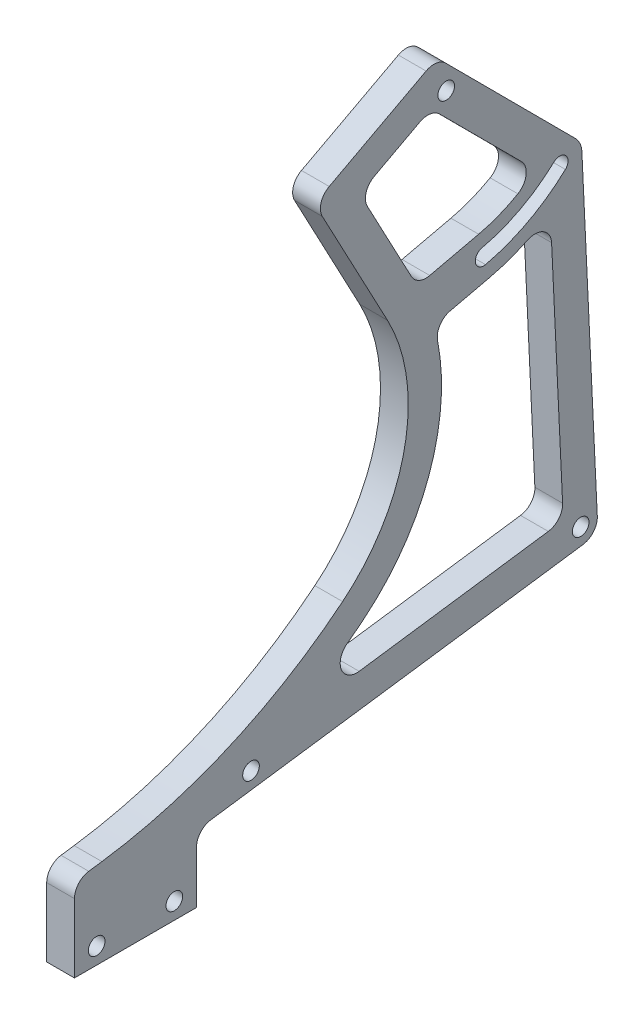
SolidWorks part; units mm, degrees
ref_plane "Front Plane" through (0, 0, 0) normal (0, 0, 1) x (1, 0, 0)
ref_plane "Top Plane" through (0, 0, 0) normal (0, 1, 0) x (1, 0, 0)
ref_plane "Right Plane" through (0, 0, 0) normal (1, 0, 0) x (0, 0, -1)
sketch "Sketch1" plane through (0, 0, 0) normal (1, 0, 0) x (0, 0, -1)
  line L0 (0, 0) -> (0, 15)
  line L1 (0, 15) -> (94.0755, 28.2214) construction
  line L2 (94.0755, 28.2214) -> (94.362, 22.2028)
  line L3 (94.362, 22.2028) -> (22, 12.0329)
  line L5 (22, 12.0329) -> (22, 0)
  line L6 (22, 0) -> (0, 0)
  line L11 (73.7485, 75.7689) -> (67, 105) construction
  line L12 (67, 105) -> (87.46, 83.0594) construction
  line L13 (0, 15) -> (4.9513, 15.6959)
  line L14 (65.3411, 110.9134) -> (43.2674, 99.1766)
  line L15 (43.2674, 99.1766) -> (56.4126, 74.4541)
  line L17 (65.3411, 110.9134) -> (90.2928, 85.8834)
  line L18 (67, 105) -> (81.0841, 78.5116) construction
  line L19 (49.84, 86.8153) -> (81.3511, 103.5701) construction
  line L20 (91.4554, 83.2496) -> (94.0755, 28.2214)
  line L21 (37.7341, 20.3032) -> (88.1086, 27.3829)
  line L22 (88.1086, 27.3829) -> (85.763, 76.646)
  line L23 (83.1087, 84.5914) -> (64.2314, 103.5279)
  line L24 (64.2314, 103.5279) -> (51.382, 96.6957)
  line L25 (51.382, 96.6957) -> (61.7937, 77.1141)
  line L26 (61.7937, 77.1141) -> (72.8487, 79.6664)
  line L27 (64.7746, 69.5919) -> (74.6483, 71.8714)
  circle A0 centre (4, 3) radius 1.5
  circle A1 centre (18, 3) radius 1.5
  arc A2 (56.4126, 74.4541) -> (48.3259, 34.5861) centre (28.1583, 59.431) cw
  arc A3 (52.1073, 29.9276) -> (64.7746, 69.5919) centre (28.1583, 59.431) ccw
  circle A4 centre (67, 105) radius 1.5
  arc A5 (87.46, 83.0594) -> (73.7485, 75.7689) centre (67, 105) cw construction
  arc A6 (74.086, 74.3073) -> (88.4829, 81.9624) centre (67, 105) ccw
  arc A7 (73.4111, 77.2305) -> (86.437, 84.1564) centre (67, 105) ccw
  arc A8 (73.4111, 77.2305) -> (74.086, 74.3073) centre (73.7485, 75.7689) ccw
  arc A9 (88.4829, 81.9624) -> (86.437, 84.1564) centre (87.46, 83.0594) ccw
  arc A10 (74.6483, 71.8714) -> (85.763, 76.646) centre (67, 105) ccw
  arc A11 (48.3259, 34.5861) -> (4.9513, 15.6959) centre (-7.3415, 103.1641) cw
  arc A12 (37.7341, 20.3032) -> (52.1073, 29.9276) centre (-7.3415, 103.1641) ccw
  circle A13 centre (73.7485, 75.7689) radius 4 construction
  arc A15 (72.8487, 79.6664) -> (83.1087, 84.5914) centre (67, 105) ccw
  arc A17 (90.2928, 85.8834) -> (91.4554, 83.2496) centre (87.46, 83.0594) cw
  point P15 (0, 0)
  point P24 (81.0841, 78.5116)
  dimension "D8" = 105
  dimension "D9" = 95
  dimension "D10" = 4
  dimension "D11" = 3
  dimension "D12" = 30
  dimension "D14" = 67
  dimension "D21" = 6
  dimension "D23" = 25
  dimension "D24" = 6
  dimension "D25" = 1.5
  dimension "D26" = 8
  dimension "D32" = 4
  dimension "D33" = 8
  dimension "D30" = 32
  dimension "D18" = 4
  dimension "D5" = 3
  dimension "D1" = 6
  dimension "D4" = 22
  dimension "D6" = 15
  dimension "D7" = 4
  dimension "D13" = 3
  dimension "D15" = 62
  dimension "D16" = 30
  dimension "D17" = 6
  dimension "D19" = 28
  dimension "D20" = 3
  dimension "D22" = 5
  dimension "D27" = 12
  dimension "D28" = 6
  dimension "D29" = 6
  dimension "D31" = 6
extrude "Boss-Extrude1" add sketch "Sketch1" along normal blind 5
fillet "Fillet1" radius 3 13 edges at (2.5, 27.3829, -88.1086) (2.5, 20.3032, -37.7341) (2.5, 84.5914, -83.1087) (2.5, 110.9134, -65.3411) (2.5, 103.5279, -64.2314) (2.5, 96.6957, -51.382) (2.5, 77.1141, -61.7937) (2.5, 15, 0) (2.5, 76.646, -85.763) (2.5, 99.1766, -43.2674) (2.5, 22.2028, -94.362) (2.5, 12.0329, -22) (2.5, 69.5919, -64.7746)
sketch "Sketch7" plane through (5, 0, 0) normal (1, 0, 0) x (0, 0, -1)
  line L0 (4.9513, 15.6959) -> (2.5825, 15.3629) construction
  line L3 (51.3131, 22.2116) -> (85.3994, 27.0021) construction
  line L4 (94.2319, 24.9355) -> (91.4554, 83.2496) construction
  circle A0 centre (31.8192, 16.4424) radius 1.5
  circle A1 centre (91.2353, 24.7928) radius 1.5
  dimension "D1" = 3
  dimension "D4" = 60
  dimension "D2" = 3
  dimension "D3" = 3
  dimension "D5" = 3
extrude "Cut-Extrude2" cut sketch "Sketch7" against normal up to next
equation "\"ˇ3\"=3.9176"
